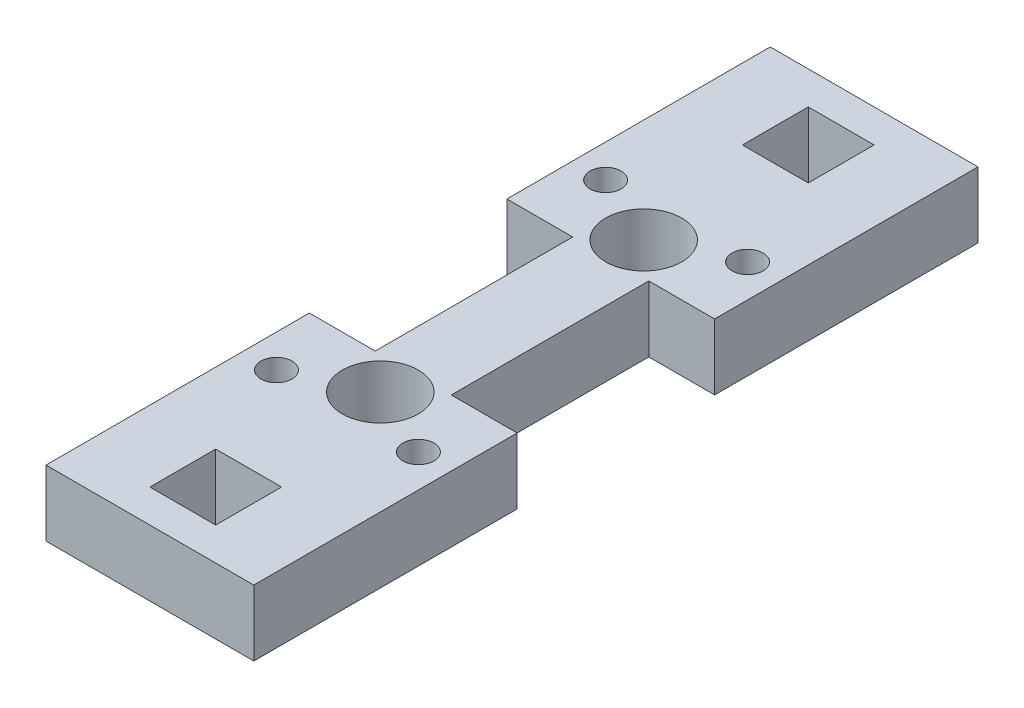
SolidWorks part; units mm, degrees
ref_plane "Front Plane" through (0, 0, 0) normal (0, 0, 1) x (1, 0, 0)
ref_plane "Top Plane" through (0, 0, 0) normal (0, 1, 0) x (1, 0, 0)
ref_plane "Right Plane" through (0, 0, 0) normal (1, 0, 0) x (0, 0, -1)
sketch "Sketch1" plane through (0, 0, 0) normal (0, 1, 0) x (1, 0, 0)
  line L0 (3.175, 44.45) -> (3.175, 63.5) construction
  line L1 (0, 0) -> (20.0406, 0)
  line L2 (0, 0) -> (0, 69.85)
  line L3 (0, 69.85) -> (20.0406, 69.85)
  line L4 (20.0406, 0) -> (20.0406, 69.85)
  line L5 (6.8453, 66.675) -> (13.1953, 66.675)
  line L6 (6.8453, 66.675) -> (6.8453, 60.325)
  line L7 (6.8453, 60.325) -> (13.1953, 60.325)
  line L8 (13.1953, 66.675) -> (13.1953, 60.325)
  line L9 (13.6906, 44.45) -> (20.0406, 44.45)
  line L10 (13.6906, 44.45) -> (13.6906, 25.4)
  line L11 (13.6906, 25.4) -> (20.0406, 25.4)
  line L12 (20.0406, 44.45) -> (20.0406, 25.4)
  line L13 (13.1953, 3.175) -> (6.8453, 3.175)
  line L14 (13.1953, 3.175) -> (13.1953, 9.525)
  line L15 (13.1953, 9.525) -> (6.8453, 9.525)
  line L16 (6.8453, 3.175) -> (6.8453, 9.525)
  line L17 (0, 44.45) -> (6.35, 44.45)
  line L18 (0, 44.45) -> (0, 25.4)
  line L19 (0, 25.4) -> (6.35, 25.4)
  line L20 (6.35, 44.45) -> (6.35, 25.4)
  line L21 (3.175, 63.5) -> (6.8453, 63.5) construction
  line L22 (13.1953, 63.5) -> (16.8656, 63.5) construction
  line L23 (16.8656, 63.5) -> (16.8656, 44.45) construction
  line L24 (16.8656, 25.4) -> (16.8656, 6.35) construction
  line L25 (16.8656, 6.35) -> (13.1953, 6.35) construction
  line L26 (6.8453, 6.35) -> (3.175, 6.35) construction
  line L27 (3.175, 6.35) -> (3.175, 25.4) construction
  line L28 (10.0203, 69.85) -> (10.0203, 66.675) construction
  line L29 (10.0203, 66.675) -> (10.0203, 47.625) construction
  line L30 (10.0203, 47.625) -> (10.0203, 22.225) construction
  line L31 (10.0203, 22.225) -> (10.0203, 9.525) construction
  line L32 (10.0203, 9.525) -> (10.0203, 3.175) construction
  line L33 (10.0203, 3.175) -> (10.0203, 0) construction
  line L35 (0, 34.925) -> (6.35, 34.925) construction
  line L36 (6.35, 34.925) -> (10.0203, 34.925) construction
  line L37 (10.0203, 34.925) -> (13.6906, 34.925) construction
  line L38 (13.6906, 34.925) -> (20.0406, 34.925) construction
  circle A0 centre (10.0203, 47.625) radius 3.6703
  circle A1 centre (10.0203, 22.225) radius 3.6703
  dimension "D8" = 7.3406
  dimension "D1" = 6.35
  dimension "D3" = 6.35
  dimension "D4" = 57.15
  dimension "D6" = 69.85
  dimension "D7" = 25.4
  dimension "D9" = 19.05
extrude "Boss-Extrude1" add sketch "Sketch1" along normal blind 6.35 contours L17 L20 L19 L2 L1 L4 L11 L10 L9 L3 A1 A0 L13 L16 L15 L14 L5 L8 L7 L6
sketch "Sketch2" plane through (0, 6.35, 0) normal (0, 1, 0) x (1, 0, 0)
  line L0 (10.0203, 69.85) -> (10.0203, 0) construction
  line L1 (0, 69.85) -> (20.0406, 69.85) construction
  line L2 (0, 0) -> (20.0406, 0) construction
  line L5 (10.0203, 34.925) -> (-9.9372, 34.925) construction
  line L6 (0, 44.45) -> (6.35, 44.45) construction
  line L7 (3.175, 34.925) -> (3.175, 52.0119) construction
  circle A0 centre (3.175, 50.8) radius 1.5
  circle A1 centre (3.175, 19.05) radius 1.5
  circle A2 centre (16.8656, 19.05) radius 1.5
  circle A3 centre (16.8656, 50.8) radius 1.5
  point P8 (3.175, 44.45)
  point P13 (3.175, 50.8)
  dimension "D2" = 3
  dimension "D1" = 15.875
extrude "Cut-Extrude1" cut sketch "Sketch2" against normal through all
